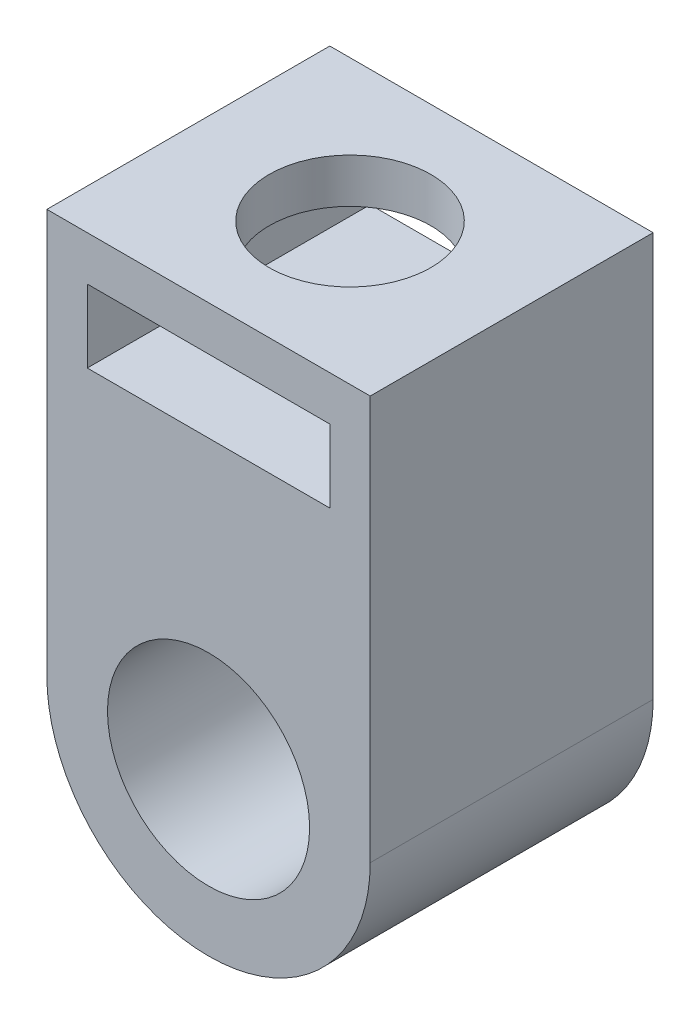
SolidWorks part; units mm, degrees
ref_plane "Front Plane" through (0, 0, 0) normal (0, 0, 1) x (1, 0, 0)
ref_plane "Top Plane" through (0, 0, 0) normal (0, 1, 0) x (1, 0, 0)
ref_plane "Right Plane" through (0, 0, 0) normal (1, 0, 0) x (0, 0, -1)
sketch "Sketch2" plane through (0, 0, 0) normal (0, 0, 1) x (1, 0, 0)
  line L2 (-4, 0) -> (-4, 10)
  line L3 (-4, 10) -> (4, 10)
  line L4 (4, 0) -> (4, 10)
  arc A0 (-4, 0) -> (4, 0) centre (0, 0) ccw
  circle A1 centre (0, 0) radius 2.5
  dimension "D1" = 8
  dimension "D3" = 5
  dimension "D2" = 10
extrude "Boss-Extrude1" add sketch "Sketch2" along normal blind 7
sketch "Sketch3" plane through (0, 0, 7) normal (0, 0, 1) x (1, 0, 0)
  line L0 (4, 10) -> (-4, 10) construction
  line L1 (3, 8.9) -> (-3, 8.9)
  line L2 (3, 8.9) -> (3, 7.1)
  line L3 (3, 7.1) -> (-3, 7.1)
  line L4 (-3, 8.9) -> (-3, 7.1)
  line L5 (3, 8.9) -> (-3, 7.1) construction
  line L6 (3, 7.1) -> (-3, 8.9) construction
  point P0 (0, 8)
  dimension "D1" = 2
  dimension "D2" = 6
  dimension "D3" = 1.8
extrude "Cut-Extrude1" cut sketch "Sketch3" against normal blind 7
sketch "Sketch4" plane through (0, 10, 0) normal (0, 1, 0) x (1, 0, 0)
  circle A0 centre (0, -3.5) radius 2
  dimension "D1" = 4
extrude "Cut-Extrude2" cut sketch "Sketch4" against normal blind 2
